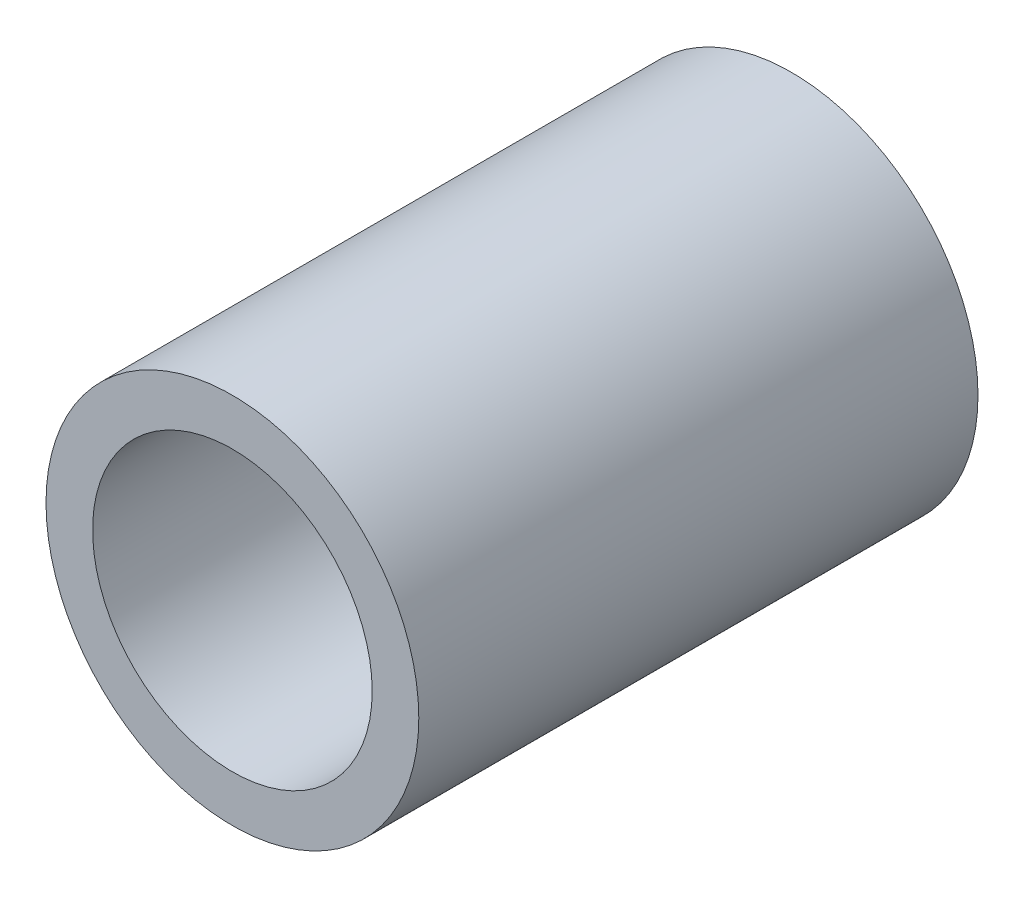
SolidWorks part; units mm, degrees
material "Сталь"
ref_plane "Спереди" through (0, 0, 0) normal (0, 0, 1) x (1, 0, 0)
ref_plane "Сверху" through (0, 0, 0) normal (0, 1, 0) x (1, 0, 0)
ref_plane "Справа" through (0, 0, 0) normal (1, 0, 0) x (0, 0, -1)
sketch "Эскиз1" plane through (0, 0, 0) normal (0, 0, 1) x (1, 0, 0)
  circle A0 centre (0, 0) radius 6
  circle A1 centre (0, 0) radius 8
  dimension "D1" = 12
  dimension "D2" = 16
extrude "Бобышка-Вытянуть1" add sketch "Эскиз1" along normal blind 24
